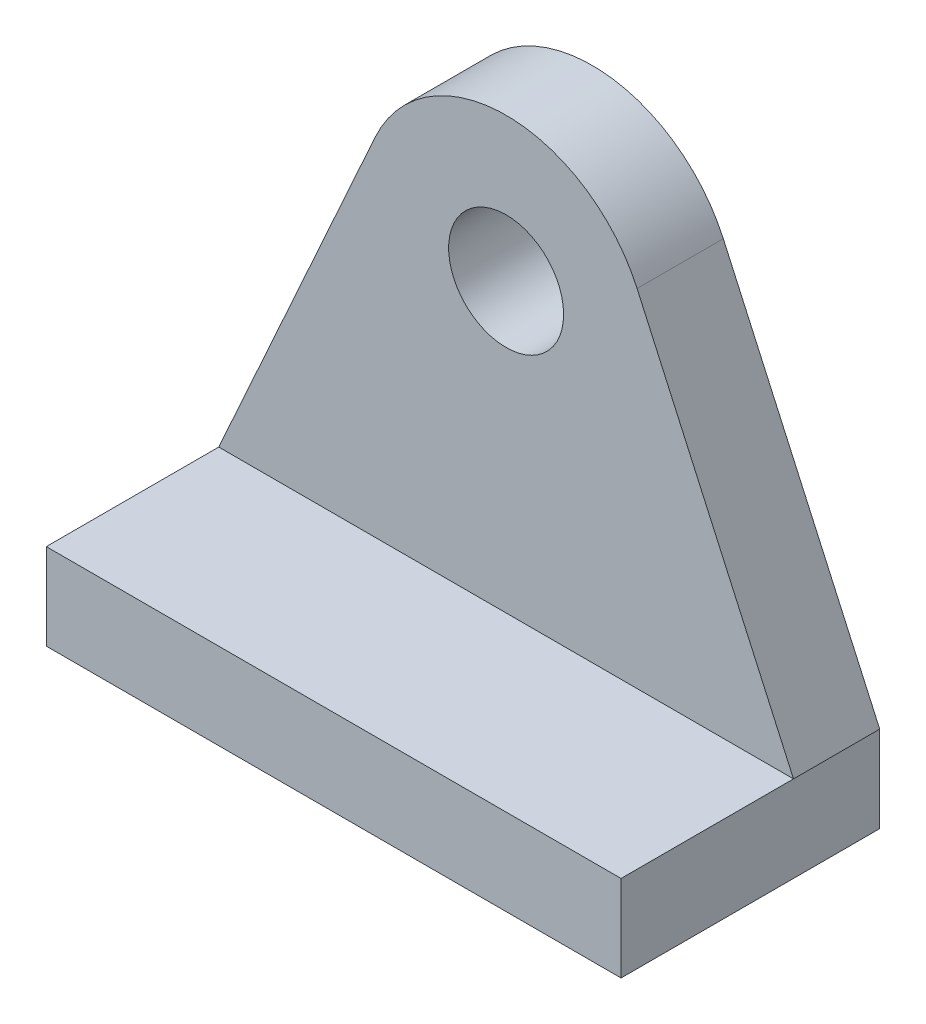
SolidWorks part; units mm, degrees
ref_plane "前视基准面" through (0, 0, 0) normal (0, 0, 1) x (1, 0, 0)
ref_plane "上视基准面" through (0, 0, 0) normal (0, 1, 0) x (1, 0, 0)
ref_plane "右视基准面" through (0, 0, 0) normal (1, 0, 0) x (0, 0, -1)
sketch "草图1" plane through (0, 0, 0) normal (0, 0, 1) x (1, 0, 0)
  line L1 (0, -10) -> (-10, -10)
  line L2 (0, -10) -> (10, -10)
  line L3 (-10, -10) -> (-4.5572, 2.0572)
  line L4 (10, -10) -> (4.5572, 2.0572)
  circle A0 centre (0, 0) radius 2
  arc A1 (4.5572, 2.0572) -> (-4.5572, 2.0572) centre (0, 0) ccw
  dimension "D1" = 4
  dimension "D2" = 10
  dimension "D3" = 10
  dimension "D4" = 10
  dimension "D5" = 10
extrude "凸台-拉伸1" add sketch "草图1" along normal blind 3
sketch "草图2" plane through (0, 0, 0) normal (0, 0, -1) x (-1, 0, 0)
  line L1 (-10, -10) -> (10, -10)
  line L2 (-10, -10) -> (-10, -13)
  line L3 (-10, -13) -> (10, -13)
  line L4 (10, -10) -> (10, -13)
  dimension "D1" = 3
extrude "凸台-拉伸2" add sketch "草图2" against normal blind 9
ref_plane "基准面1" through (0, 0, 0) normal (0, 1, 0) x (-1, 0, 0)
